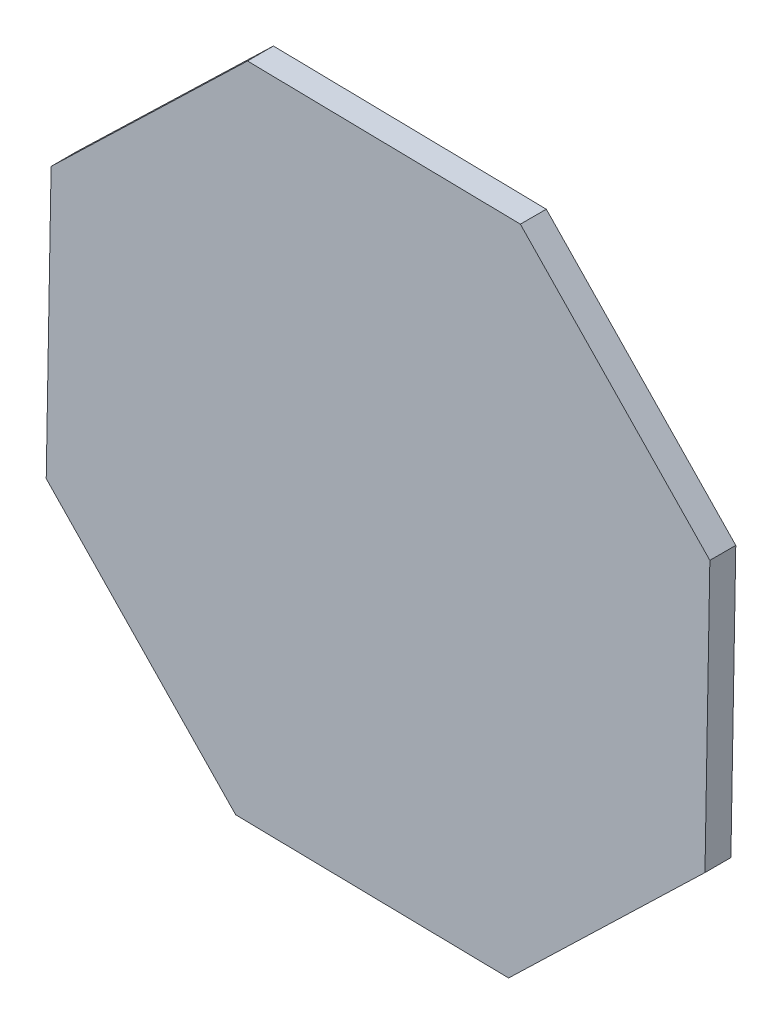
SolidWorks part; units mm, degrees
ref_plane "Front Plane" through (0, 0, 0) normal (0, 0, 1) x (1, 0, 0)
ref_plane "Top Plane" through (0, 0, 0) normal (0, 1, 0) x (1, 0, 0)
ref_plane "Right Plane" through (0, 0, 0) normal (1, 0, 0) x (0, 0, -1)
sketch "Sketch1" plane through (0, 0, 0) normal (0, 0, 1) x (1, 0, 0)
  line L1 (-130.0027, -51.1408) -> (-55.7638, -128.0878)
  line L2 (-55.7638, -128.0878) -> (51.1408, -130.0027)
  line L3 (51.1408, -130.0027) -> (128.0878, -55.7638)
  line L4 (128.0878, -55.7638) -> (130.0027, 51.1408)
  line L5 (130.0027, 51.1408) -> (55.7638, 128.0878)
  line L6 (55.7638, 128.0878) -> (-51.1408, 130.0027)
  line L7 (-51.1408, 130.0027) -> (-128.0878, 55.7638)
  line L8 (-128.0878, 55.7638) -> (-130.0027, -51.1408)
  circle A0 centre (0, 0) radius 139.7 construction
extrude "Boss-Extrude1" add sketch "Sketch1" along normal mid plane 10.16
equation "\"Material\"= \"MDF@FinalBot.assembly\""
equation "\"D1@Boss-Extrude1\" = \"Material\""
